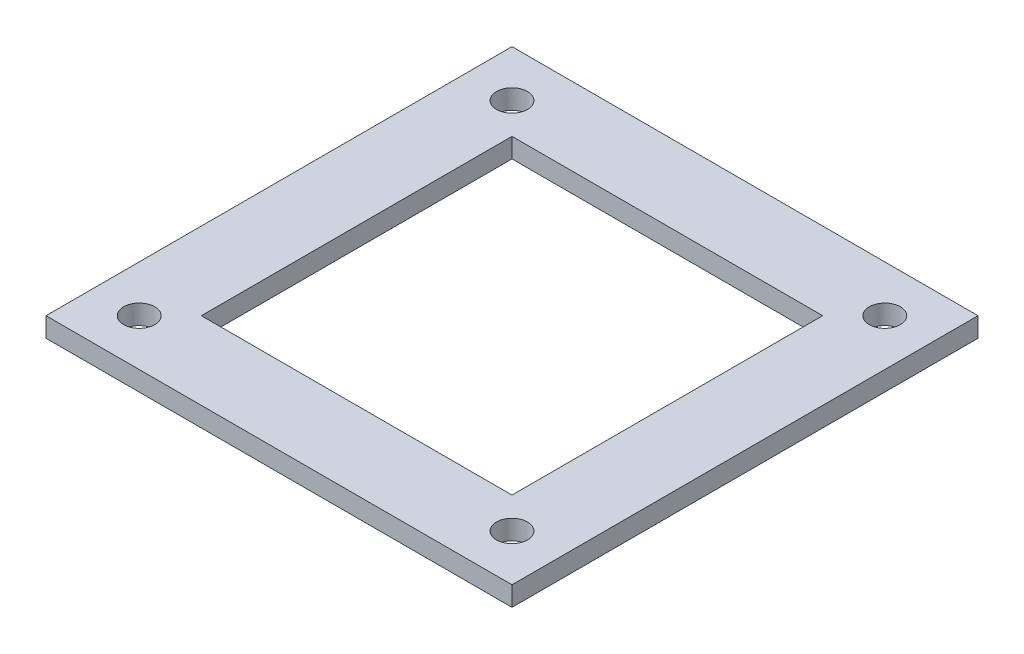
SolidWorks part; units mm, degrees
ref_plane "Front Plane" through (0, 0, 0) normal (0, 0, 1) x (1, 0, 0)
ref_plane "Top Plane" through (0, 0, 0) normal (0, 1, 0) x (1, 0, 0)
ref_plane "Right Plane" through (0, 0, 0) normal (1, 0, 0) x (0, 0, -1)
sketch "Sketch1" plane through (0, 0, 0) normal (0, 1, 0) x (1, 0, 0)
  line L0 (0, 0) -> (38.1, 38.1) construction
  line L1 (38.1, 38.1) -> (38.1, -38.1) construction
  line L2 (38.1, -38.1) -> (0, 0) construction
  line L3 (0, 0) -> (-38.1, -38.1) construction
  line L4 (-38.1, -38.1) -> (38.1, -38.1) construction
  line L5 (-38.1, -38.1) -> (-38.1, 38.1) construction
  line L6 (-38.1, 38.1) -> (38.1, 38.1) construction
  line L7 (38.1, 38.1) -> (0, 0) construction
  line L8 (0, 0) -> (-38.1, 38.1) construction
  line L10 (47.625, -47.625) -> (-47.625, -47.625)
  line L11 (47.625, -47.625) -> (47.625, 47.625)
  line L12 (47.625, 47.625) -> (-47.625, 47.625)
  line L13 (-47.625, -47.625) -> (-47.625, 47.625)
  line L14 (47.625, -47.625) -> (-47.625, 47.625) construction
  line L15 (47.625, 47.625) -> (-47.625, -47.625) construction
  line L16 (31.75, -31.75) -> (-31.75, -31.75)
  line L17 (31.75, -31.75) -> (31.75, 31.75)
  line L18 (31.75, 31.75) -> (-31.75, 31.75)
  line L19 (-31.75, -31.75) -> (-31.75, 31.75)
  line L20 (31.75, -31.75) -> (-31.75, 31.75) construction
  line L21 (31.75, 31.75) -> (-31.75, -31.75) construction
  circle A0 centre (-38.1, 38.1) radius 3.175
  circle A1 centre (38.1, 38.1) radius 3.175
  circle A2 centre (38.1, -38.1) radius 3.175
  circle A3 centre (-38.1, -38.1) radius 3.175
  dimension "D1" = 6.35
  dimension "D2" = 6.35
  dimension "D3" = 6.35
  dimension "D4" = 6.35
  dimension "D5" = 76.2
  dimension "D6" = 95.25
  dimension "D7" = 95.25
  dimension "D8" = 63.5
extrude "Boss-Extrude1" add sketch "Sketch1" along normal blind 4
